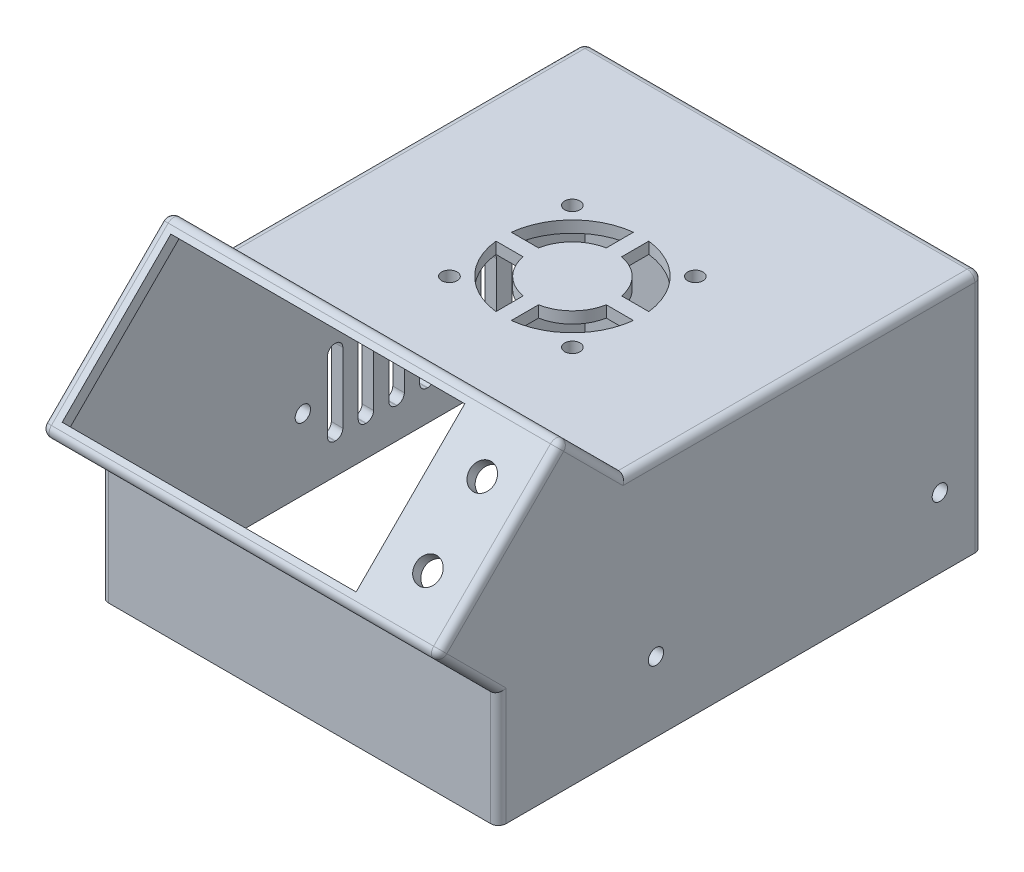
SolidWorks part; units mm, degrees
ref_plane "Front Plane" through (0, 0, 0) normal (0, 0, 1) x (1, 0, 0)
ref_plane "Top Plane" through (0, 0, 0) normal (0, 1, 0) x (1, 0, 0)
ref_plane "Right Plane" through (0, 0, 0) normal (1, 0, 0) x (0, 0, -1)
sketch "Sketch1" plane through (0, 0, 0) normal (0, 1, 0) x (1, 0, 0)
  line L1 (0, 0) -> (97.5, 0)
  line L2 (0, 0) -> (0, 120)
  line L3 (0, 120) -> (97.5, 120)
  line L4 (97.5, 0) -> (97.5, 120)
  line L5 (-3, 123) -> (100.5, 123)
  line L6 (-3, 123) -> (-3, -3)
  line L7 (-3, -3) -> (100.5, -3)
  line L8 (100.5, 123) -> (100.5, -3)
  dimension "D1" = 120
  dimension "D2" = 97.5
  dimension "D3" = 3
  dimension "D4" = 3
  dimension "D5" = 3
  dimension "D6" = 3
extrude "Boss-Extrude1" add sketch "Sketch1" along normal blind 60
sketch "Sketch2" plane through (0, 60, 0) normal (0, 1, 0) x (1, 0, 0)
  line L0 (-3, -3) -> (100.5, -3) construction
  line L1 (-3, 123) -> (100.5, 123)
  line L2 (-3, 123) -> (-3, -3)
  line L3 (-3, -3) -> (100.5, -3)
  line L4 (100.5, 123) -> (100.5, -3)
  line L5 (100.5, -3) -> (100.5, 123) construction
extrude "Boss-Extrude2" add sketch "Sketch2" along normal blind 3
sketch "Sketch4" plane through (100.5, 0, 0) normal (1, 0, 0) x (0, 0, -1)
  line L0 (-3, 63) -> (-3, 29.766)
  line L1 (-3, 63) -> (-3, 0) construction
  line L2 (-3, 29.766) -> (30.234, 63)
  line L3 (-3, 63) -> (123, 63) construction
  line L4 (30.234, 63) -> (-3, 63)
  dimension "D1" = 47
  dimension "D2" = 45
extrude "Cut-Extrude1" cut sketch "Sketch4" against normal up to next
sketch "Sketch5" plane through (0, 16.383, 16.383) normal (0, 0.7071, 0.7071) x (1, 0, 0)
  line L1 (-3, 65.9264) -> (100.5, 65.9264)
  line L2 (-3, 65.9264) -> (-3, 18.9264)
  line L3 (-3, 18.9264) -> (100.5, 18.9264)
  line L4 (100.5, 65.9264) -> (100.5, 18.9264)
  line L5 (0, 62.9264) -> (97.5, 62.9264)
  line L6 (0, 62.9264) -> (0, 21.9264)
  line L7 (0, 21.9264) -> (97.5, 21.9264)
  line L8 (97.5, 62.9264) -> (97.5, 21.9264)
  dimension "D1" = 97.5
  dimension "D2" = 3
  dimension "D3" = 3
  dimension "D4" = 3
extrude "Boss-Extrude4" add sketch "Sketch5" along normal blind 20
sketch "Sketch6" plane through (0, 16.383, 16.383) normal (0, 0.7071, 0.7071) x (1, 0, 0)
  line L1 (0, 62.9264) -> (97.5, 62.9264)
  line L2 (0, 62.9264) -> (0, 21.9264)
  line L3 (0, 21.9264) -> (97.5, 21.9264)
  line L4 (97.5, 62.9264) -> (97.5, 21.9264)
extrude "Cut-Extrude2" cut sketch "Sketch6" against normal blind 3
sketch "Sketch7" plane through (0, 30.5251, 30.5251) normal (0, 0.7071, 0.7071) x (1, 0, 0)
  line L0 (88.875, 52.4264) -> (88.875, 32.4264) construction
  line L1 (-3, 65.9264) -> (100.5, 65.9264)
  line L2 (-3, 65.9264) -> (-3, 18.9264)
  line L3 (-3, 18.9264) -> (100.5, 18.9264)
  line L4 (100.5, 65.9264) -> (100.5, 18.9264)
  line L5 (0.75, 62.4264) -> (77.25, 62.4264)
  line L6 (0.75, 62.4264) -> (0.75, 22.4264)
  line L7 (0.75, 22.4264) -> (77.25, 22.4264)
  line L8 (77.25, 62.4264) -> (77.25, 22.4264)
  line L9 (77.25, 42.4264) -> (100.5, 42.4264) construction
  circle A0 centre (88.875, 52.4264) radius 3.25
  circle A1 centre (88.875, 32.4264) radius 3.25
  point P10 (0.75, 42.4264)
  point P11 (-3, 42.4264)
  point P16 (88.875, 42.4264)
  point P17 (77.25, 42.4264)
  point P20 (88.875, 42.4264)
  dimension "D4" = 6.5
  dimension "D5" = 6.5
  dimension "D1" = 40
  dimension "D2" = 3.75
  dimension "D3" = 76.5
  dimension "D6" = 20
extrude "Boss-Extrude5" add sketch "Sketch7" along normal blind 3
sketch "Sketch8" plane through (0, 0, -123) normal (0, 0, -1) x (-1, 0, 0)
  line L0 (-100.5, 63) -> (3, 63) construction
  line L1 (-46.25, 58) -> (-22.75, 58)
  line L2 (-48.25, 56) -> (-48.25, 41)
  line L3 (-46.25, 39) -> (-22.75, 39)
  line L4 (-20.75, 56) -> (-20.75, 41)
  line L5 (3, 63) -> (-100.5, 63) construction
  line L6 (-85, 48.5) -> (-12.5, 48.5) construction
  line L9 (-100.5, 0) -> (3, 0) construction
  line L10 (3, 63) -> (3, 0) construction
  arc A0 (-48.25, 41) -> (-46.25, 39) centre (-46.25, 41) ccw
  arc A1 (-22.75, 39) -> (-20.75, 41) centre (-22.75, 41) ccw
  arc A2 (-20.75, 56) -> (-22.75, 58) centre (-22.75, 56) ccw
  arc A3 (-46.25, 58) -> (-48.25, 56) centre (-46.25, 56) ccw
  circle A5 centre (-54.5, 48.5) radius 2
  circle A6 centre (-14.5, 48.5) radius 2
  circle A7 centre (-74.5, 48.5) radius 10.5
  circle A8 centre (-44, 28.7) radius 2
  point P6 (-48.25, 39)
  point P11 (-20.75, 58)
  point P14 (-48.25, 58)
  point P17 (-48.25, 48.5)
  point P18 (-48.75, 63)
  point P26 (-34.5, 58)
  point P28 (-48.75, 48.5)
  dimension "D3" = 2
  dimension "D4" = 21
  dimension "D9" = 20
  dimension "D10" = 4
  dimension "D11" = 4
  dimension "D13" = 4
  dimension "D1" = 19
  dimension "D2" = 27.5
  dimension "D5" = 20
  dimension "D6" = 28.7
  dimension "D7" = 5
  dimension "D8" = 20
  dimension "D12" = 47
extrude "Cut-Extrude3" cut sketch "Sketch8" against normal up to next
sketch "Sketch10" plane through (0, 63, 0) normal (0, 1, 0) x (1, 0, 0)
  line L0 (100.5, 123) -> (-3, 123) construction
  line L5 (46.75, 85.8885) -> (46.75, 78.8167)
  line L6 (50.75, 85.8885) -> (50.75, 78.8167)
  line L7 (30.8615, 70) -> (37.9333, 70)
  line L8 (30.8615, 66) -> (37.9333, 66)
  line L9 (-3, 123) -> (-3, 30.234) construction
  line L15 (46.75, 57.1833) -> (46.75, 50.1115)
  line L16 (59.5667, 66) -> (66.6385, 66)
  line L18 (50.75, 57.1833) -> (50.75, 50.1115)
  line L20 (59.5667, 70) -> (66.6385, 70)
  circle A0 centre (32.75, 84) radius 2
  circle A1 centre (64.75, 84) radius 2
  circle A2 centre (32.75, 52) radius 2
  circle A3 centre (64.75, 52) radius 2
  arc A4 (30.8615, 66) -> (46.75, 50.1115) centre (48.75, 68) ccw
  arc A5 (46.75, 78.8167) -> (37.9333, 70) centre (48.75, 68) ccw
  arc A6 (37.9333, 66) -> (46.75, 57.1833) centre (48.75, 68) ccw
  arc A7 (46.75, 85.8885) -> (30.8615, 70) centre (48.75, 68) ccw
  arc A8 (59.5667, 70) -> (50.75, 78.8167) centre (48.75, 68) ccw
  arc A9 (66.6385, 70) -> (50.75, 85.8885) centre (48.75, 68) ccw
  arc A10 (50.75, 57.1833) -> (59.5667, 66) centre (48.75, 68) ccw
  arc A11 (50.75, 50.1115) -> (66.6385, 66) centre (48.75, 68) ccw
  dimension "D8" = 4
  dimension "D9" = 4
  dimension "D10" = 4
  dimension "D11" = 4
  dimension "D12" = 36
  dimension "D13" = 22
  dimension "D4" = 32
  dimension "D5" = 32
  dimension "D6" = 51.75
  dimension "D7" = 55
extrude "Cut-Extrude5" cut sketch "Sketch10" against normal up to next
sketch "Sketch11" plane through (0, 60, 0) normal (0, -1, 0) x (1, 0, 0)
  line L6 (97.5, -28.9914) -> (97.5, -120) construction
  line L7 (97.5, -28.9914) -> (0, -28.9914) construction
  line L8 (97.5, 0) -> (97.5, -120) construction
  circle A0 centre (81.1, -47.0914) radius 1
  circle A1 centre (81.1, -47.0914) radius 3
  circle A2 centre (92.8, -79.9914) radius 1
  circle A3 centre (92.8, -79.9914) radius 3
  dimension "D7" = 2
  dimension "D8" = 6
  dimension "D11" = 2
  dimension "D12" = 6
  dimension "D2" = 16.4
  dimension "D3" = 18.1
  dimension "D4" = 4.7
  dimension "D5" = 51
extrude "Boss-Extrude6" add sketch "Sketch11" along normal blind 5
sketch "Sketch12" plane through (100.5, 0, 0) normal (1, 0, 0) x (0, 0, -1)
  line L0 (-3, 0) -> (123, 0) construction
  line L1 (123, 63) -> (123, 0) construction
  circle A0 centre (111.9, 18.2) radius 2
  circle A1 centre (38, 18.2) radius 2
  dimension "D3" = 4
  dimension "D6" = 4
  dimension "D1" = 18.2
  dimension "D2" = 11.1
  dimension "D4" = 18.2
  dimension "D5" = 85
extrude "Cut-Extrude6" cut sketch "Sketch12" against normal up to next
sketch "Sketch13" plane through (-3, 0, 0) normal (-1, 0, 0) x (0, 0, 1)
  line L0 (-123, 0) -> (3, 0) construction
  line L1 (-123, 63) -> (-123, 0) construction
  line L2 (-97.0059, 28.1) -> (-97.0059, 9.9)
  line L3 (-103.1059, 30) -> (-102.9059, 30)
  line L4 (-105.0059, 28.1) -> (-105.0059, 9.9)
  line L5 (-103.1059, 8) -> (-102.9059, 8)
  line L6 (-101.0059, 28.1) -> (-101.0059, 9.9)
  line L7 (-95.1059, 30) -> (-94.9059, 30)
  line L8 (-93.0059, 28.1) -> (-93.0059, 9.9)
  line L9 (-95.1059, 8) -> (-94.9059, 8)
  line L10 (-89.0059, 28.1) -> (-89.0059, 9.9)
  line L11 (-87.1059, 30) -> (-86.9059, 30)
  line L12 (-85.0059, 28.1) -> (-85.0059, 9.9)
  line L13 (-87.1059, 8) -> (-86.9059, 8)
  line L14 (-81.0059, 28.1) -> (-81.0059, 9.9)
  line L15 (-79.1059, 30) -> (-78.9059, 30)
  line L16 (-77.0059, 28.1) -> (-77.0059, 9.9)
  line L17 (-79.1059, 8) -> (-78.9059, 8)
  line L18 (-73.0059, 28.1) -> (-73.0059, 9.9)
  line L19 (-71.1059, 30) -> (-70.9059, 30)
  line L20 (-69.0059, 28.1) -> (-69.0059, 9.9)
  line L21 (-71.1059, 8) -> (-70.9059, 8)
  line L22 (-65.0059, 28.1) -> (-65.0059, 9.9)
  line L23 (-63.1059, 30) -> (-62.9059, 30)
  line L24 (-61.0059, 28.1) -> (-61.0059, 9.9)
  line L25 (-63.1059, 8) -> (-62.9059, 8)
  line L26 (-57.0059, 28.1) -> (-57.0059, 9.9)
  line L27 (-55.1059, 30) -> (-54.9059, 30)
  line L28 (-53.0059, 28.1) -> (-53.0059, 9.9)
  line L29 (-55.1059, 8) -> (-54.9059, 8)
  circle A0 centre (-112.8, 18.4) radius 2
  circle A1 centre (-46.6, 18.4) radius 2
  arc A2 (-102.9059, 8) -> (-101.0059, 9.9) centre (-102.9059, 9.9) ccw
  arc A3 (-105.0059, 9.9) -> (-103.1059, 8) centre (-103.1059, 9.9) ccw
  arc A4 (-102.9059, 30) -> (-101.0059, 28.1) centre (-102.9059, 28.1) cw
  arc A5 (-103.1059, 30) -> (-105.0059, 28.1) centre (-103.1059, 28.1) ccw
  arc A6 (-95.1059, 30) -> (-97.0059, 28.1) centre (-95.1059, 28.1) ccw
  arc A7 (-97.0059, 9.9) -> (-95.1059, 8) centre (-95.1059, 9.9) ccw
  arc A8 (-94.9059, 30) -> (-93.0059, 28.1) centre (-94.9059, 28.1) cw
  arc A9 (-94.9059, 8) -> (-93.0059, 9.9) centre (-94.9059, 9.9) ccw
  arc A10 (-87.1059, 30) -> (-89.0059, 28.1) centre (-87.1059, 28.1) ccw
  arc A11 (-89.0059, 9.9) -> (-87.1059, 8) centre (-87.1059, 9.9) ccw
  arc A12 (-86.9059, 30) -> (-85.0059, 28.1) centre (-86.9059, 28.1) cw
  arc A13 (-86.9059, 8) -> (-85.0059, 9.9) centre (-86.9059, 9.9) ccw
  arc A14 (-79.1059, 30) -> (-81.0059, 28.1) centre (-79.1059, 28.1) ccw
  arc A15 (-81.0059, 9.9) -> (-79.1059, 8) centre (-79.1059, 9.9) ccw
  arc A16 (-78.9059, 30) -> (-77.0059, 28.1) centre (-78.9059, 28.1) cw
  arc A17 (-78.9059, 8) -> (-77.0059, 9.9) centre (-78.9059, 9.9) ccw
  arc A18 (-71.1059, 30) -> (-73.0059, 28.1) centre (-71.1059, 28.1) ccw
  arc A19 (-73.0059, 9.9) -> (-71.1059, 8) centre (-71.1059, 9.9) ccw
  arc A20 (-70.9059, 30) -> (-69.0059, 28.1) centre (-70.9059, 28.1) cw
  arc A21 (-70.9059, 8) -> (-69.0059, 9.9) centre (-70.9059, 9.9) ccw
  arc A22 (-63.1059, 30) -> (-65.0059, 28.1) centre (-63.1059, 28.1) ccw
  arc A23 (-65.0059, 9.9) -> (-63.1059, 8) centre (-63.1059, 9.9) ccw
  arc A24 (-62.9059, 30) -> (-61.0059, 28.1) centre (-62.9059, 28.1) cw
  arc A25 (-62.9059, 8) -> (-61.0059, 9.9) centre (-62.9059, 9.9) ccw
  arc A26 (-55.1059, 30) -> (-57.0059, 28.1) centre (-55.1059, 28.1) ccw
  arc A27 (-57.0059, 9.9) -> (-55.1059, 8) centre (-55.1059, 9.9) ccw
  arc A28 (-54.9059, 30) -> (-53.0059, 28.1) centre (-54.9059, 28.1) cw
  arc A29 (-54.9059, 8) -> (-53.0059, 9.9) centre (-54.9059, 9.9) ccw
  point P16 (-105.0059, 8)
  point P19 (-101.0059, 30)
  point P22 (-105.0059, 30)
  dimension "D3" = 4
  dimension "D6" = 4
  dimension "D10" = 1.9
  dimension "D1" = 18.4
  dimension "D2" = 10.2
  dimension "D4" = 18.4
  dimension "D5" = 76.4
  dimension "D7" = 22
  dimension "D8" = 4
  dimension "D9" = 8
  dimension "D11" = 7
extrude "Cut-Extrude7" cut sketch "Sketch13" against normal blind 5
fillet "Fillet2" radius 2 8 edges at (100.5, 71.1317, -22.1023) (48.75, 79.2635, -13.9706) (-3, 71.1317, -22.1023) (-3, 62.6464, 2.6464) (-3, 37.8977, 11.1317) (100.5, 37.8977, 11.1317) (48.75, 46.0294, 19.2635) (100.5, 62.6464, 2.6464)
fillet "Fillet3" radius 2 7 edges at (100.5, 31.5, -123) (100.5, 63, -75.2028) (100.5, 16.2972, 3) (-3, 16.2972, 3) (-3, 31.5, -123) (48.75, 63, -123) (-3, 63, -75.2028)
